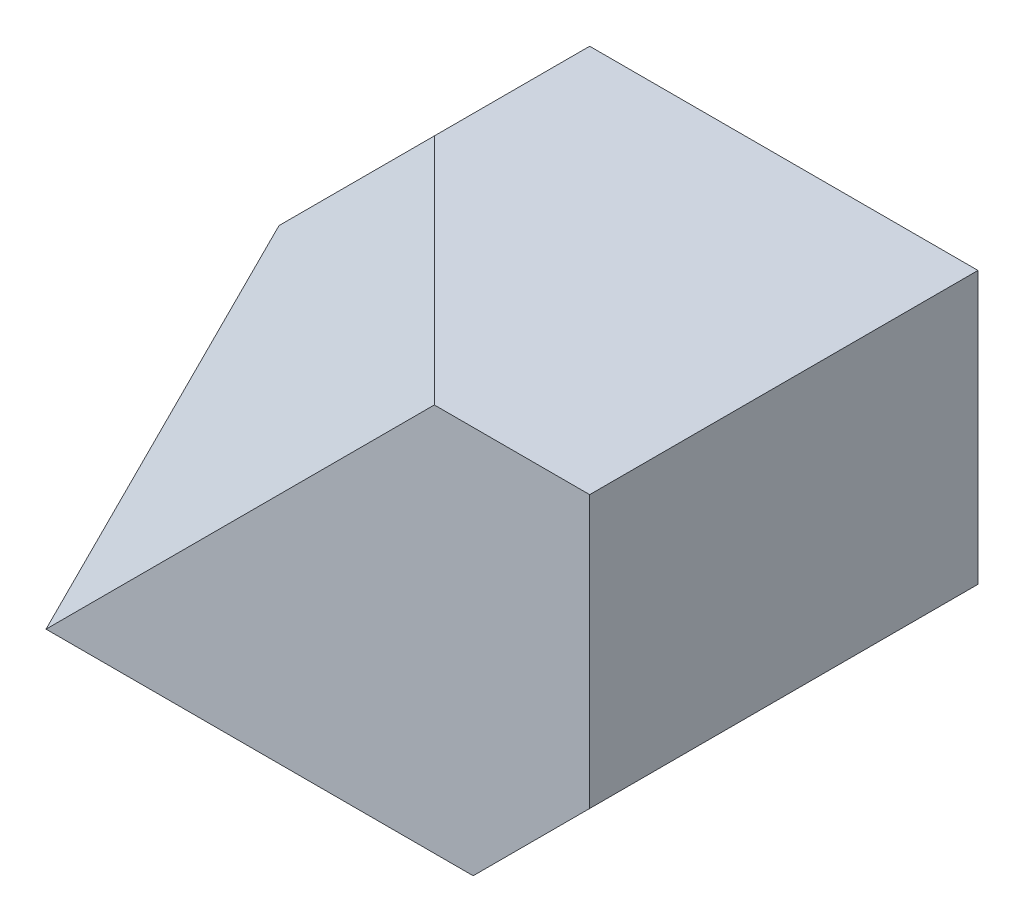
SolidWorks part; units mm, degrees
ref_plane "Front Plane" through (0, 0, 0) normal (0, 0, 1) x (1, 0, 0)
ref_plane "Top Plane" through (0, 0, 0) normal (0, 1, 0) x (1, 0, 0)
ref_plane "Right Plane" through (0, 0, 0) normal (1, 0, 0) x (0, 0, -1)
sketch "Sketch1" plane through (0, 0, 0) normal (0, 0, 1) x (1, 0, 0)
  line L0 (0, 0) -> (0, 30)
  line L1 (0, 0) -> (55, 0)
  line L2 (55, 0) -> (70, 15)
  line L3 (70, 15) -> (70, 50)
  line L4 (70, 50) -> (20, 50)
  line L5 (20, 50) -> (0, 30)
  dimension "D1" = 55
  dimension "D2" = 15
  dimension "D3" = 15
  dimension "D4" = 35
  dimension "D5" = 50
  dimension "D6" = 20
extrude "Boss-Extrude1" add sketch "Sketch1" along normal blind 50
sketch "Sketch2" plane through (0, 0, 50) normal (0, 0, 1) x (1, 0, 0)
  line L0 (0, 0) -> (50, 50)
  line L1 (70, 50) -> (20, 50) construction
  line L2 (50, 50) -> (20, 50)
  line L3 (20, 50) -> (0, 30) construction
  line L4 (20, 50) -> (0, 30)
  line L5 (0, 30) -> (0, 0)
  dimension "D1" = 20
extrude "Cut-Extrude2" cut sketch "Sketch2" against normal blind 30
sketch "Sketch4" plane through (0, 0, 0) normal (0, 0, -1) x (-1, 0, 0)
  line L0 (-55, 0) -> (-55, 15)
  line L1 (-70, 15) -> (-55, 15)
  line L2 (-55, 0) -> (-70, 15)
  line M6 (-70, 15) -> (-55, 0)
  dimension "D1" = 15
  dimension "D2" = 15
extrude "Cut-Extrude3" cut sketch "Sketch4" against normal blind 15 contours L1 L0 M6
ref_plane "Plane2" through (13.3333, -13.3333, -13.3333) normal (0.5774, -0.5774, -0.5774) x (-0.8165, -0.4082, -0.4082)
sketch "Sketch7" plane through (13.3333, -13.3333, -13.3333) normal (0.5774, -0.5774, -0.5774) x (-0.8165, -0.4082, -0.4082)
  line L0 (-51.031, -10.6066) -> (-69.4022, 0)
  line L1 (-69.4022, 0) -> (-51.031, 10.6066)
  line L2 (-51.031, 10.6066) -> (-51.031, -10.6066)
extrude "Boss-Extrude4" add sketch "Sketch7" against normal blind 15
sketch "Sketch11" plane through (0, 0, 0) normal (-1, 0, 0) x (0, 0, 1)
  line L0 (20, 30) -> (50, 0)
  line L1 (50, 0) -> (20, 0)
  line L2 (20, 0) -> (20, 30)
  dimension "D1" = 30
  dimension "D2" = 30
extrude "Boss-Extrude6" add sketch "Sketch11" against normal blind 52
sketch "Sketch12" plane through (0, 50, 0) normal (0, 1, 0) x (1, 0, 0)
  line L0 (20, -20) -> (50, -50)
  line L1 (50, -50) -> (50, -20)
  line L2 (50, -20) -> (20, -20)
extrude "Boss-Extrude7" add sketch "Sketch12" against normal blind 52
sketch "Sketch13" plane through (0, 0, 0) normal (0, -1, 0) x (1, 0, 0)
  line L0 (20, 20) -> (50, 20)
  line L1 (50, 20) -> (50, 50)
  line L2 (50, 50) -> (20, 20)
extrude "Cut-Extrude6" cut sketch "Sketch13" along normal blind 52
ref_plane "Plane4" through (-16.6667, 16.6667, 16.6667) normal (0.5774, -0.5774, -0.5774) x (-0.8165, -0.4082, -0.4082)
sketch "Sketch14" plane through (-16.6667, 16.6667, 16.6667) normal (0.5774, -0.5774, -0.5774) x (-0.8165, -0.4082, -0.4082)
  line L0 (-20.4124, 7.0711) -> (-44.9073, 21.2132)
  line L1 (-44.9073, 21.2132) -> (-81.6497, 0)
  line L2 (-81.6497, 0) -> (-20.4124, 7.0711)
extrude "Boss-Extrude8" add sketch "Sketch14" along normal blind 30
ref_plane "Plane5" through (-16.6667, 16.6667, 16.6667) normal (-0.5774, 0.5774, 0.5774) x (0.8165, 0.4082, 0.4082)
sketch "Sketch15" plane through (-16.6667, 16.6667, 16.6667) normal (-0.5774, 0.5774, 0.5774) x (0.8165, 0.4082, 0.4082)
  line L0 (20.4124, -35.3553) -> (81.6497, 0)
  line L1 (81.6497, 0) -> (20.4124, 7.0711)
  line L2 (20.4124, 7.0711) -> (20.4124, -35.3553)
extrude "Boss-Extrude9" add sketch "Sketch15" against normal blind 15
sketch "Sketch16" plane through (0, 0, 0) normal (0, -1, 0) x (1, 0, 0)
  line L0 (0, 50) -> (8.6603, 32.6795)
  line L1 (8.6603, 32.6795) -> (17.3205, 41.3397)
  line L2 (17.3205, 41.3397) -> (0, 50)
extrude "Cut-Extrude7" cut sketch "Sketch16" along normal blind 15
sketch "Sketch17" plane through (0, 0, 0) normal (0, -1, 0) x (-1, 0, 0)
  line L0 (0, 0) -> (-20, -20)
  line L1 (-20, -20) -> (-20, 0)
  line L2 (0, 0) -> (-55, 0) construction
  line L3 (-20, 0) -> (0, 0)
  dimension "D1" = 20
  dimension "D2" = 20
extrude "Cut-Extrude8" cut sketch "Sketch17" against normal blind 15
